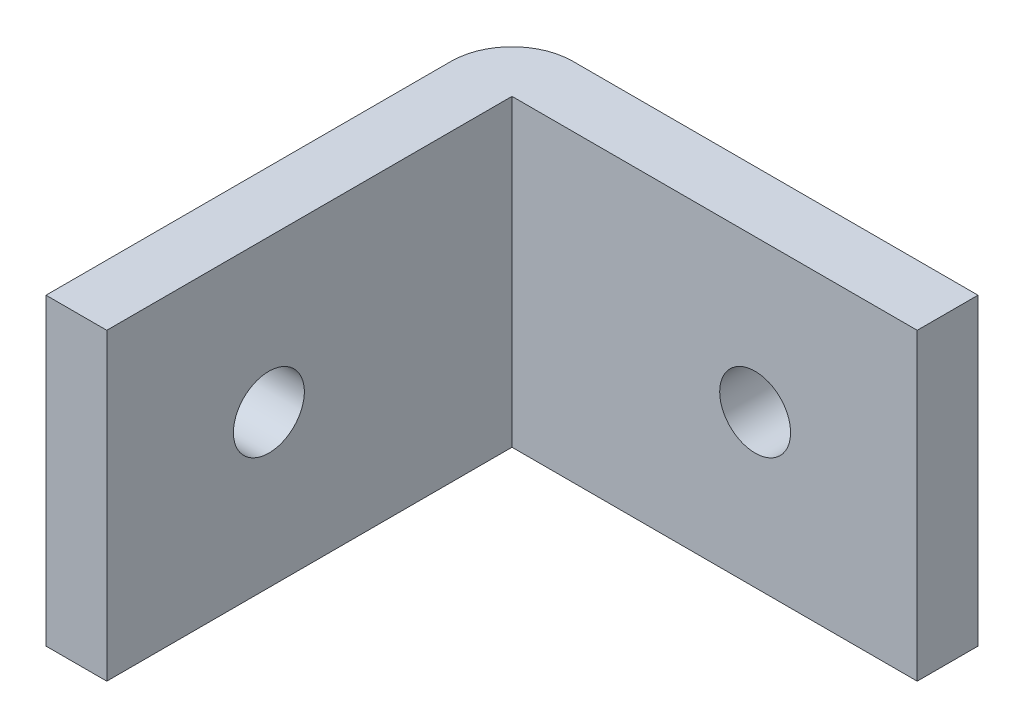
SolidWorks part; units mm, degrees
ref_plane "Front Plane" through (0, 0, 0) normal (0, 0, 1) x (1, 0, 0)
ref_plane "Top Plane" through (0, 0, 0) normal (0, 1, 0) x (1, 0, 0)
ref_plane "Right Plane" through (0, 0, 0) normal (1, 0, 0) x (0, 0, -1)
sketch "Sketch1" plane through (0, 0, 0) normal (0, 0, 1) x (1, 0, 0)
  line L1 (-11.5, -7.5) -> (11.5, -7.5)
  line L2 (-11.5, -7.5) -> (-11.5, 7.5)
  line L3 (-11.5, 7.5) -> (11.5, 7.5)
  line L4 (11.5, -7.5) -> (11.5, 7.5)
  line L5 (-11.5, -7.5) -> (11.5, 7.5) construction
  line L6 (-11.5, 7.5) -> (11.5, -7.5) construction
  point P0 (0, 0)
  dimension "D1" = 23
  dimension "D2" = 15
extrude "Boss-Extrude1" add sketch "Sketch1" along normal blind 3
sketch "Sketch10" plane through (0, 0, 3) normal (0, 0, 1) x (1, 0, 0)
  line L0 (-11.5, -7.5) -> (11.5, -7.5) construction
  line L1 (-11.5, 7.5) -> (-8.5, 7.5)
  line L2 (-11.5, 7.5) -> (-11.5, -7.5)
  line L3 (-11.5, -7.5) -> (-8.5, -7.5)
  line L4 (-8.5, 7.5) -> (-8.5, -7.5)
  dimension "D1" = 3
extrude "Boss-Extrude2" add sketch "Sketch10" along normal blind 20
sketch "Sketch13" plane through (0, 0, 0) normal (0, 0, -1) x (-1, 0, 0)
  line L0 (11.5, 7.5) -> (11.5, -7.5) construction
  circle A0 centre (-3.5, 0) radius 1.75
  dimension "D1" = 3.5
  dimension "D2" = 15
extrude "Cut-Extrude3" cut sketch "Sketch13" against normal through all
sketch "Sketch14" plane through (-11.5, 0, 0) normal (-1, 0, 0) x (0, 0, 1)
  circle A0 centre (15, 0) radius 1.75
  dimension "D1" = 3.5
  dimension "D2" = 15
extrude "Cut-Extrude4" cut sketch "Sketch14" against normal through all
fillet "Fillet1" radius 3 1 edges at (-11.5, 0, 0)
sketch "Bend-Lines1" plane through (0, 0, 0) normal (0, 1, 0) x (1, 0, 0)
sketch "Bounding-Box1" plane through (0, 0, 0) normal (0, 1, 0) x (1, 0, 0)
